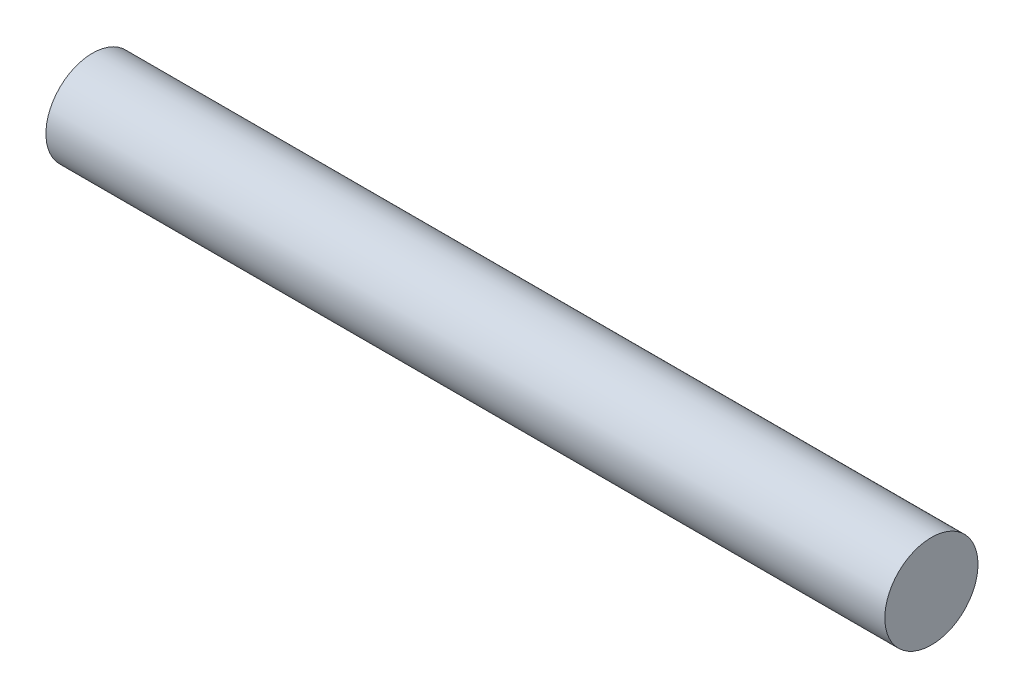
SolidWorks part; units mm, degrees
material "Plain Carbon Steel"
ref_plane "Front Plane" through (0, 0, 0) normal (0, 0, 1) x (1, 0, 0)
ref_plane "Top Plane" through (0, 0, 0) normal (0, 1, 0) x (1, 0, 0)
ref_plane "Right Plane" through (0, 0, 0) normal (1, 0, 0) x (0, 0, -1)
sketch "Sketch1" plane through (0, 0, 0) normal (1, 0, 0) x (0, 0, -1)
  circle A0 centre (0, 0) radius 9.525
extrude "Boss-Extrude1" add sketch "Sketch1" along normal blind 171.45
